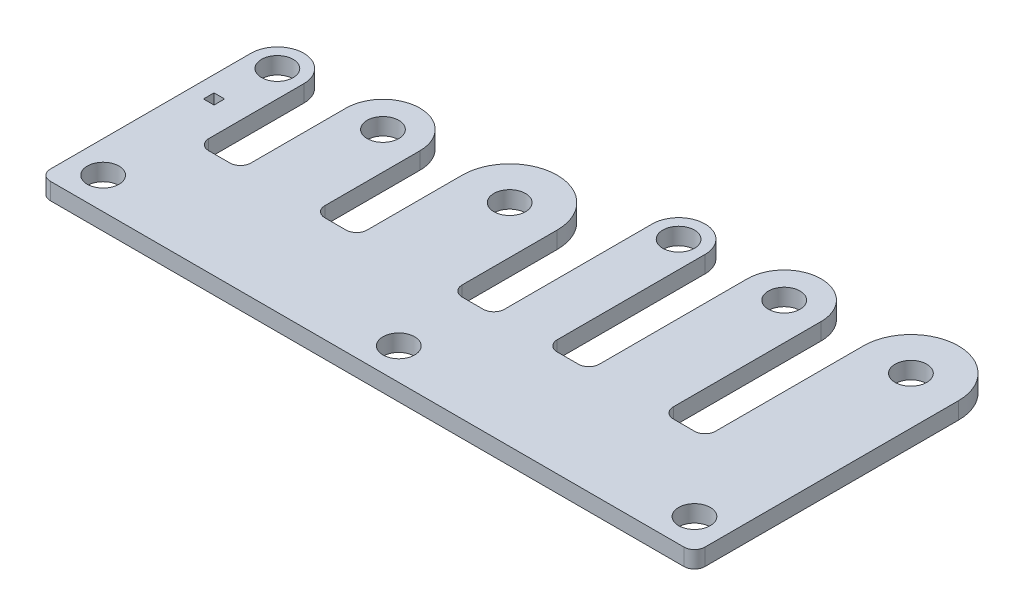
SolidWorks part; units mm, degrees
ref_plane "Front Plane" through (0, 0, 0) normal (0, 0, 1) x (1, 0, 0)
ref_plane "Top Plane" through (0, 0, 0) normal (0, 1, 0) x (1, 0, 0)
ref_plane "Right Plane" through (0, 0, 0) normal (1, 0, 0) x (0, 0, -1)
sketch "Sketch1" plane through (0, 0, 0) normal (0, 1, 0) x (1, 0, 0)
  line L0 (6.5, 5) -> (6.5, -5)
  line L1 (-2.5, 5) -> (2.5, 5) construction
  line L2 (-2.5, 5) -> (-2.5, -5)
  line L3 (-2.5, -5) -> (2.5, -5)
  line L4 (2.5, 5) -> (2.5, -5)
  line L5 (-2.5, 5) -> (2.5, -5) construction
  line L6 (-2.5, -5) -> (2.5, 5) construction
  line L7 (-2.5, -5) -> (59.5, -5)
  line L8 (-2.5, -5) -> (-2.5, -15)
  line L9 (-2.5, -15) -> (59.5, -15)
  line L10 (59.5, -5) -> (59.5, -15)
  line L11 (13.5, 5) -> (13.5, -5)
  line L12 (17.5, 5) -> (17.5, -5)
  line L13 (26.5, 5) -> (26.5, -5)
  line L14 (30.5, 10) -> (30.5, -5)
  line L15 (35.5, 10) -> (35.5, -5)
  line L16 (39.5, 10) -> (39.5, -5)
  line L17 (46.5, 10) -> (46.5, -5)
  line L18 (50.5, 10) -> (50.5, -5)
  line L19 (59.5, 10) -> (59.5, -5)
  line L20 (2.5, 5) -> (6.5, 5) construction
  line L21 (13.5, 5) -> (17.5, 5) construction
  line L22 (26.5, 5) -> (30.5, 5) construction
  line L23 (35.5, 10) -> (39.5, 10) construction
  line L24 (46.5, 10) -> (50.5, 10) construction
  line L25 (0, 5) -> (0, -1) construction
  line L26 (0, -1) -> (-1, -1)
  line L27 (-1.778, 2.81) -> (1.778, 2.81) construction
  line L28 (-1.778, 2.81) -> (-1.778, -4.81) construction
  line L29 (-1.778, -4.81) -> (1.778, -4.81) construction
  line L30 (1.778, 2.81) -> (1.778, -4.81) construction
  line L31 (-1.778, 2.81) -> (1.778, -4.81) construction
  line L32 (-1.778, -4.81) -> (1.778, 2.81) construction
  line L33 (-1, -1) -> (-1, 0)
  line L34 (-1, 0) -> (0, 0)
  line L35 (0, 0) -> (0, -1)
  circle A0 centre (0, 5) radius 1.5
  arc A1 (2.5, 5) -> (-2.5, 5) centre (0, 5) ccw
  arc A2 (13.5, 5) -> (6.5, 5) centre (10, 5) ccw
  circle A3 centre (10, 5) radius 1.5
  arc A4 (26.5, 5) -> (17.5, 5) centre (22, 5) ccw
  circle A5 centre (22, 5) radius 1.5
  arc A6 (35.5, 10) -> (30.5, 10) centre (33, 10) ccw
  circle A7 centre (33, 10) radius 1.5
  arc A8 (46.5, 10) -> (39.5, 10) centre (43, 10) ccw
  circle A9 centre (43, 10) radius 1.5
  arc A10 (59.5, 10) -> (50.5, 10) centre (55, 10) ccw
  circle A11 centre (55, 10) radius 1.5
  circle A12 centre (0.5, -12) radius 1.5
  circle A13 centre (56.5, -12) radius 1.5
  circle A14 centre (28.5, -12) radius 1.5
  point P0 (0, 0)
  point P49 (28.5, -5)
  dimension "D1" = 3
  dimension "D3" = 5
  dimension "D2" = 7
  dimension "D4" = 9
  dimension "D5" = 5
  dimension "D6" = 7
  dimension "D7" = 9
  dimension "D8" = 10
  dimension "D9" = 15
  dimension "D10" = 10
  dimension "D11" = 10
  dimension "D12" = 3
  dimension "D13" = 3
  dimension "D14" = 3
  dimension "D15" = 3.556
  dimension "D16" = 7.62
  dimension "D17" = 6
  dimension "D18" = 1
extrude "Boss-Extrude1" add sketch "Sketch1" along normal blind 1.6 contours L4 A1 L2 L3 A0 | L10 L7 L3 L8 L9 | L11 A2 L0 L7 A3 | L13 A4 L12 L7 A5 | L15 A6 L14 L7 A7 | L17 A8 L16 L7 A9 | L19 A10 L18 L7 A11
fillet "Fillet1" radius 1 12 edges at (6.5, 0.8, 5) (13.5, 0.8, 5) (17.5, 0.8, 5) (26.5, 0.8, 5) (30.5, 0.8, 5) (35.5, 0.8, 5) (39.5, 0.8, 5) (46.5, 0.8, 5) (50.5, 0.8, 5) (59.5, 0.8, 15) (-2.5, 0.8, 15) (2.5, 0.8, 5)
equation "\"D14@Sketch1\"=\"D13@Sketch1\""
